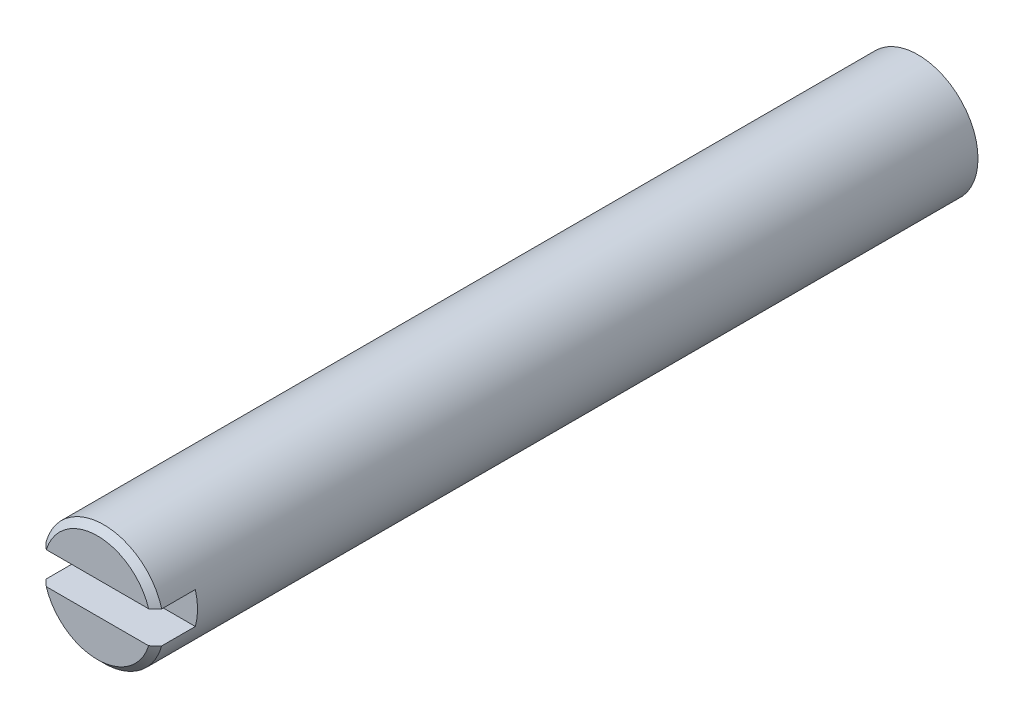
SolidWorks part; units mm, degrees
material "1023 Carbon Steel Sheet (SS)"
ref_plane "Front Plane" through (0, 0, 0) normal (0, 0, 1) x (1, 0, 0)
ref_plane "Top Plane" through (0, 0, 0) normal (0, 1, 0) x (1, 0, 0)
ref_plane "Right Plane" through (0, 0, 0) normal (1, 0, 0) x (0, 0, -1)
sketch "Sketch1" plane through (0, 0, 0) normal (0, 0, 1) x (1, 0, 0)
  circle A0 centre (0, 0) radius 4.7625
  dimension "D1" = 9.525
extrude "Boss-Extrude1" add sketch "Sketch1" along normal blind 65.1002
sketch "Sketch2" plane through (0, 0, 65.1002) normal (0, 0, 1) x (1, 0, 0)
  line L1 (-4.7625, 1.27) -> (4.7625, 1.27)
  line L2 (-4.7625, 1.27) -> (-4.7625, -1.27)
  line L3 (-4.7625, -1.27) -> (4.7625, -1.27)
  line L4 (4.7625, 1.27) -> (4.7625, -1.27)
  line L5 (-4.7625, 1.27) -> (4.7625, -1.27) construction
  line L6 (-4.7625, -1.27) -> (4.7625, 1.27) construction
  point P0 (0, 0)
  dimension "D1" = 9.525
  dimension "D2" = 2.54
extrude "Cut-Extrude1" cut sketch "Sketch2" against normal blind 3.175
chamfer "Chamfer1" distance 0.508 angle 45 2 edges at (0, 4.7625, 65.1002) (0, -4.7625, 65.1002)
